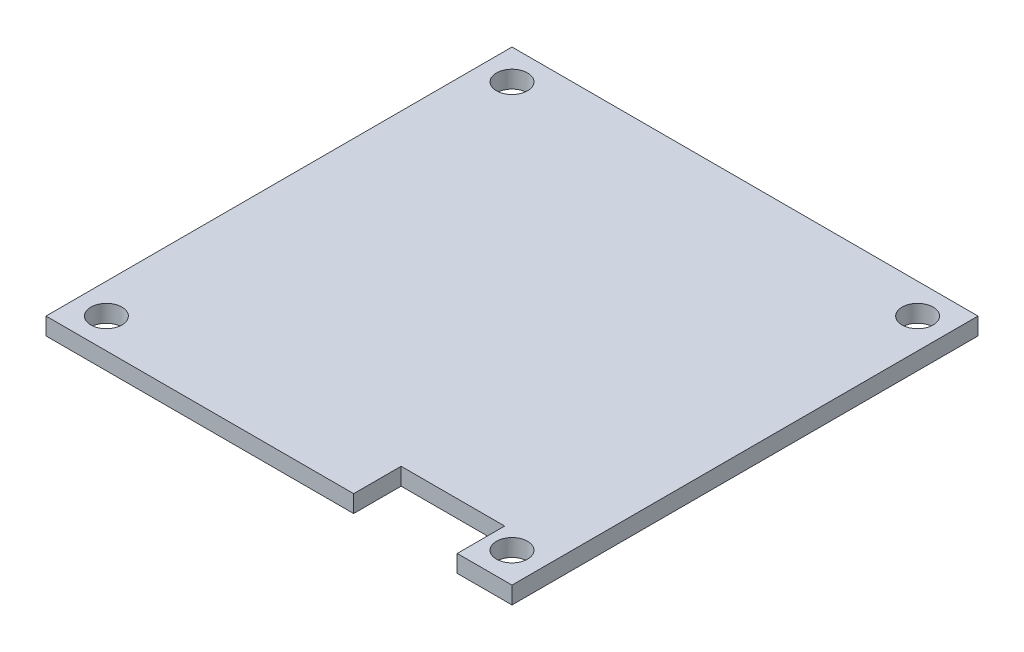
SolidWorks part; units mm, degrees
ref_plane "Front" through (0, 0, 0) normal (0, 0, 1) x (1, 0, 0)
ref_plane "Top" through (0, 0, 0) normal (0, 1, 0) x (1, 0, 0)
ref_plane "Right" through (0, 0, 0) normal (1, 0, 0) x (0, 0, -1)
sketch "草图3" plane through (0, 0, 0) normal (0, 1, 0) x (1, 0, 0)
  line L3 (-27, 27) -> (-27, -27)
  line L4 (-27, -27) -> (27, -27)
  line L5 (27, -27) -> (27, 27)
  line L6 (27, 27) -> (-27, 27)
  line L20 (8.65, -20) -> (8.65, -27)
  line L47 (20.65, -20) -> (20.65, -27)
  line L58 (8.65, -21.5) -> (20.65, -21.5)
  circle A0 centre (-23.5, -23.5) radius 1.8
  circle A1 centre (23.5, -23.5) radius 1.8
  circle A2 centre (-23.5, 23.5) radius 1.8
  circle A3 centre (23.5, 23.5) radius 1.8
  point P0 (0, 0)
  point P17 (-20, -20)
  point P23 (20, -20)
extrude "凸台-拉伸2" add sketch "草图3" along normal blind 2
